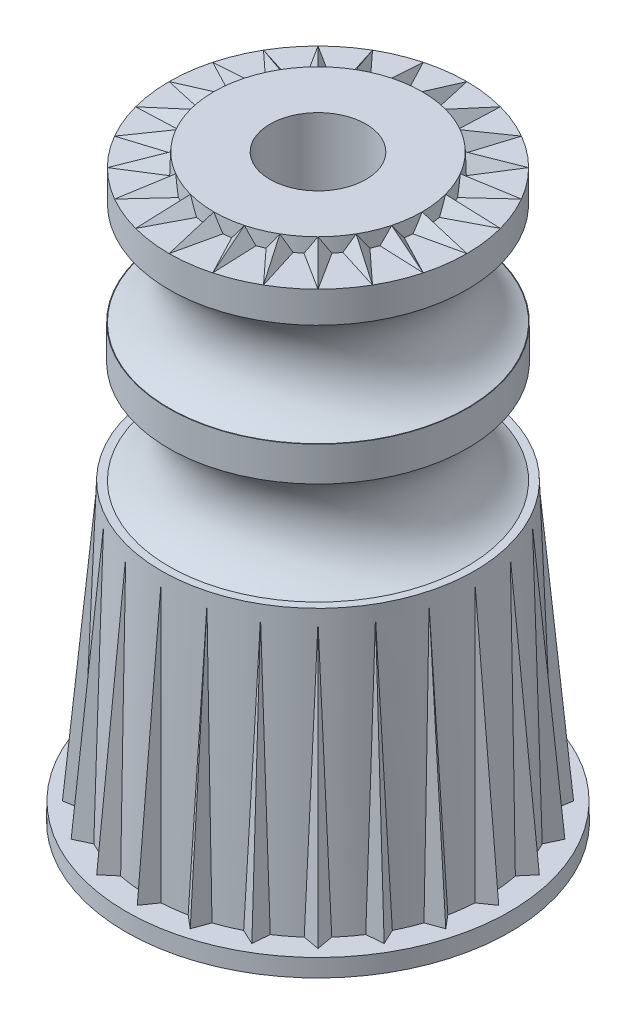
SolidWorks part; units mm, degrees
material "CA"
ref_plane "Front Plane" through (0, 0, 0) normal (0, 0, 1) x (1, 0, 0)
ref_plane "Top Plane" through (0, 0, 0) normal (0, 1, 0) x (1, 0, 0)
ref_plane "Right Plane" through (0, 0, 0) normal (1, 0, 0) x (0, 0, -1)
sketch "Sketch1" plane through (0, 0, 0) normal (0, 1, 0) x (1, 0, 0)
  circle A0 centre (0, 0) radius 8.89
  dimension "D1" = 17.78
extrude "Boss-Extrude1" add sketch "Sketch1" along normal blind 0.8128 draft 1
ref_plane "Plane1" through (0, 13.6652, 0) normal (0, 1, 0) x (1, 0, 0)
sketch "Sketch2" plane through (0, 13.6652, 0) normal (0, 1, 0) x (1, 0, 0)
  circle A0 centre (0, 0) radius 7.2517
  dimension "D1" = 14.5034
sketch "Sketch3" plane through (0, 0.8128, 0) normal (0, 1, 0) x (1, 0, 0)
  circle A0 centre (0, 0) radius 7.7343
  dimension "D1" = 15.4686
loft "Loft1" add profiles "Sketch2", "Sketch3"
sketch "Sketch4" plane through (0, 0, 0) normal (1, 0, 0) x (0, 0, -1)
  line L0 (-7.2517, 13.6652) -> (-7.7343, 0.8128) construction
  line L1 (-7.2708, 13.1572) -> (-7.7343, 0.8128) construction
  line L2 (-8.8758, 0.8128) -> (-8.89, 0) construction
  line L3 (-8.8758, 0.8128) -> (-8.89, 0) construction
  line L4 (-8.8758, 0.8128) -> (-7.2708, 13.1572) construction
  line L5 (-8.8758, 0.8128) -> (-8.3678, 0.8128) construction
  line L6 (7.2517, 13.6652) -> (-7.2517, 13.6652) construction
  line L7 (-8.3678, 0.8128) -> (-7.2708, 13.1572)
  dimension "D1" = 0.508
  dimension "D2" = 0.508
ref_plane "Plane2" through (0, 0.8128, 8.3678) normal (0, 0.9961, -0.0885) x (1, 0, 0)
sketch "Sketch14" plane through (0, 0.8128, 8.3678) normal (0, 0.9961, -0.0885) x (1, 0, 0)
  line L0 (0, 0) -> (-0.7114, 1.016)
  line L1 (0, 0) -> (0, 1.1937) construction
  line L2 (0, 0) -> (0.7114, 1.016)
  line L3 (-0.7114, 1.016) -> (0.7114, 1.016)
  dimension "D1" = 1.016
  dimension "D2" = 70
sweep "Sweep1" add profiles "Sketch14" path "Sketch4"
sketch "Sketch7" plane through (0, 0, 0) normal (1, 0, 0) x (0, 0, -1)
  line L0 (0, 0) -> (0, 29.555) construction
  line L1 (0, 0.8128) -> (0, 13.6652) construction
  line L2 (6.9215, 19.2151) -> (8.5101, 19.2151) construction
  line L3 (6.9215, 18.415) -> (6.8961, 18.415)
  line L4 (7.2517, 13.6652) -> (-7.2517, 13.6652) construction
  line L5 (6.9215, 20.0152) -> (6.9215, 18.415)
  line L6 (16.7407, 13.6652) -> (0, 13.6652) construction
  line L7 (6.8961, 13.6652) -> (0, 13.6652)
  line L8 (0, 13.6652) -> (0, 26.2128)
  line L9 (6.9215, 20.0152) -> (6.8961, 20.0152)
  line L10 (6.8961, 24.765) -> (6.8961, 26.2128)
  line L11 (6.8961, 26.2128) -> (0, 26.2128)
  arc A0 (6.8961, 20.0152) -> (6.8961, 24.765) centre (7.9415, 22.3901) cw
  arc A1 (6.8961, 18.415) -> (6.8961, 13.6652) centre (7.9415, 16.0401) ccw
  dimension "D4" = 10.6934
  dimension "D1" = 13.7922
  dimension "D2" = 0.0254
  dimension "D3" = 1.4478
  dimension "D5" = 4.7498
  dimension "D6" = 4.7498
  dimension "D7" = 1.6002
pattern_circular "CirPattern3" count 24 over 360 about axis through (0, 0, 0) along (0, 1, 0) of "Sweep1"
revolve "Revolve1" add sketch "Sketch7" angle 360 about L8
sketch "Sketch15" plane through (0, 26.2128, 0) normal (0, 1, 0) x (1, 0, 0)
  circle A0 centre (0, 0) radius 4.8768
  dimension "D1" = 9.7536
extrude "Boss-Extrude4" add sketch "Sketch15" along normal blind 0.635 draft 5
sketch "Sketch16" plane through (0, 0, 0) normal (1, 0, 0) x (0, 0, -1)
  line L0 (4.8212, 26.8478) -> (6.8961, 26.2128)
ref_plane "Plane3" through (0, 26.2128, -6.8961) normal (0, -0.2926, -0.9562) x (-1, 0, 0)
sketch "Sketch17" plane through (0, 26.2128, -6.8961) normal (0, -0.2926, -0.9562) x (-1, 0, 0)
  line L0 (0, 0) -> (0, -0.6997) construction
  line L1 (0, 0) -> (-0.5847, -0.762)
  line L2 (0, 0) -> (0.5847, -0.762)
  line L3 (-0.5847, -0.762) -> (0.5847, -0.762)
  ellipse E0 centre (0, -2.0181) end of major axis (-6.8961, -2.0181) minor radius 2.0181 construction
  dimension "D1" = 75
  dimension "D2" = 0.762
sweep "Sweep2" add profiles "Sketch17" path "Sketch16"
pattern_circular "CirPattern4" count 24 over 360 about axis through (0, 0, 0) along (0, 1, 0) of "Sweep2"
sketch "Sketch18" plane through (0, 26.8478, 0) normal (0, 1, 0) x (1, 0, 0)
  circle A0 centre (0, 0) radius 2.2225
  dimension "D1" = 4.445
extrude "Cut-Extrude1" cut sketch "Sketch18" against normal through all
sketch "Sketch19" plane through (0, 0, 0) normal (1, 0, 0) x (0, 0, -1)
  line L0 (3.2004, 0) -> (3.4123, 12.1412)
  line L1 (0, 0) -> (0, 13.0728) construction
  line L2 (0, 0.8128) -> (0, 13.6652) construction
  line L3 (7.0644, 13.6652) -> (2.6809, 13.6652) construction
  line L4 (7.2517, 13.6652) -> (-7.2517, 13.6652) construction
  line L5 (3.4123, 12.1412) -> (5.3894, 12.1412)
  line L6 (3.2004, 0) -> (3.2004, -2.54)
  line L7 (3.2004, -2.54) -> (6.4516, -2.54)
  line L8 (5.3894, 12.1412) -> (6.4516, 0)
  line L9 (6.4516, 0) -> (6.4516, -2.54)
  circle A0 centre (0, 0) radius 3.2004 construction
  dimension "D1" = 6.4008
  dimension "D2" = 1
  dimension "D3" = 1.524
  dimension "D4" = 2.54
  dimension "D5" = 5
  dimension "D6" = 3.2512
revolve "Cut-Revolve1" cut sketch "Sketch19" angle 360 about L1
